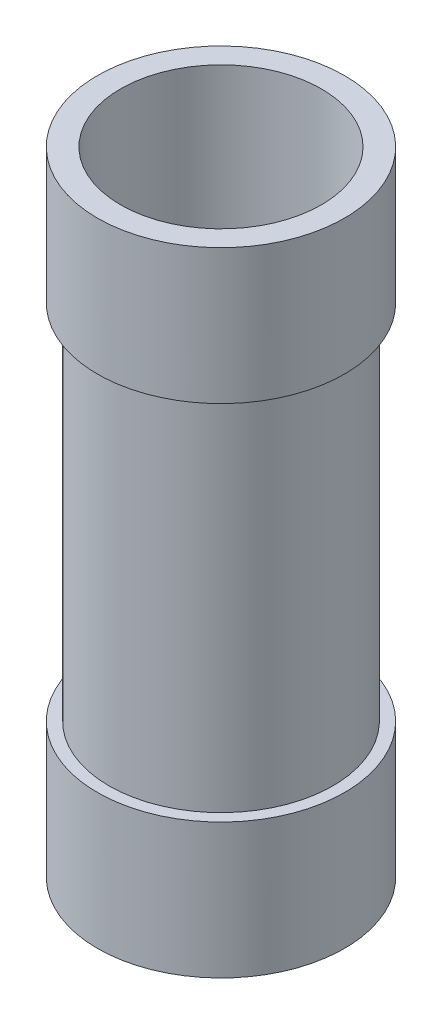
SolidWorks part; units mm, degrees
ref_plane "Front Plane" through (0, 0, 0) normal (0, 0, 1) x (1, 0, 0)
ref_plane "Top Plane" through (0, 0, 0) normal (0, 1, 0) x (1, 0, 0)
ref_plane "Right Plane" through (0, 0, 0) normal (1, 0, 0) x (0, 0, -1)
sketch "Sketch3" plane through (0, 0, 0) normal (0, 1, 0) x (1, 0, 0)
  circle A0 centre (0, 0) radius 30.5
  circle A1 centre (0, 0) radius 37.5
extrude "Boss-Extrude1" add sketch "Sketch3" along normal blind 192 contours A0 | A1
sketch "Sketch7" plane through (0, 0, 0) normal (0, -1, 0) x (-1, 0, 0)
  circle A2 centre (0, 0) radius 34
  circle A4 centre (0, 0) radius 39
extrude "Cut-Extrude3" cut sketch "Sketch7" against normal blind 110 from offset 41
